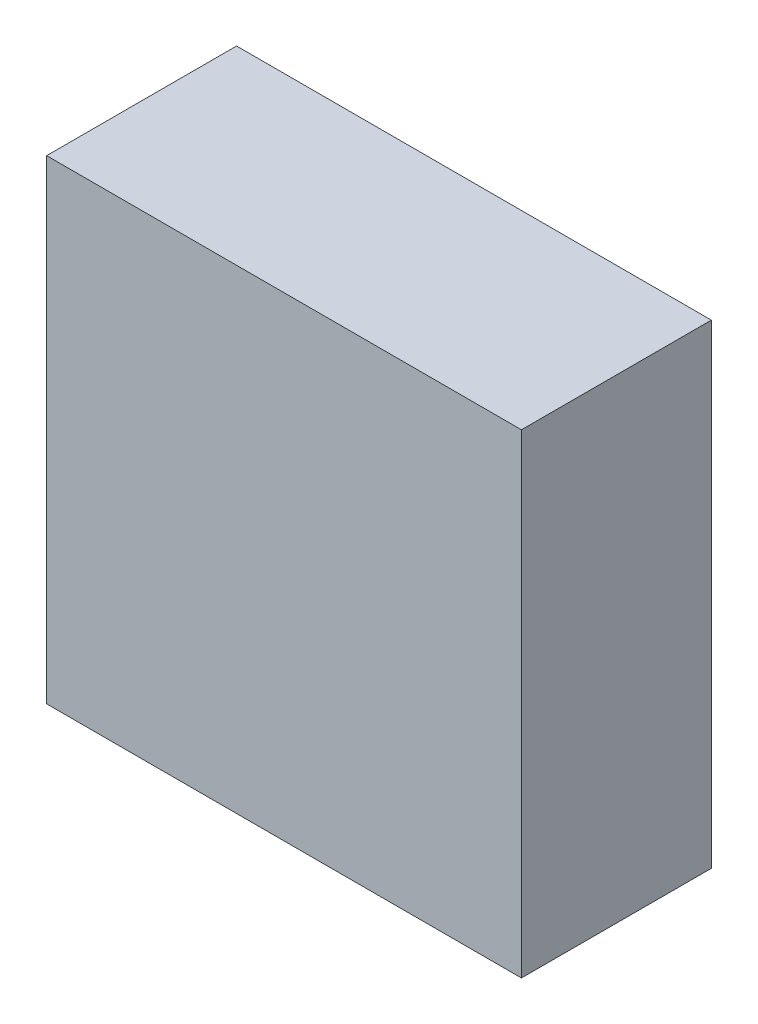
SolidWorks part; units mm, degrees
material "Acrylic (Medium-high impact)"
ref_plane "Front Plane" through (0, 0, 0) normal (0, 0, 1) x (1, 0, 0)
ref_plane "Top Plane" through (0, 0, 0) normal (0, 1, 0) x (1, 0, 0)
ref_plane "Right Plane" through (0, 0, 0) normal (1, 0, 0) x (0, 0, -1)
sketch "Sketch1" plane through (0, 0, 0) normal (0, 0, 1) x (1, 0, 0)
  line L1 (0, 0) -> (15, 0)
  line L2 (0, 0) -> (0, 15)
  line L3 (0, 15) -> (15, 15)
  line L4 (15, 0) -> (15, 15)
  dimension "D1" = 15
extrude "Boss-Extrude1" add sketch "Sketch1" along normal blind 6
